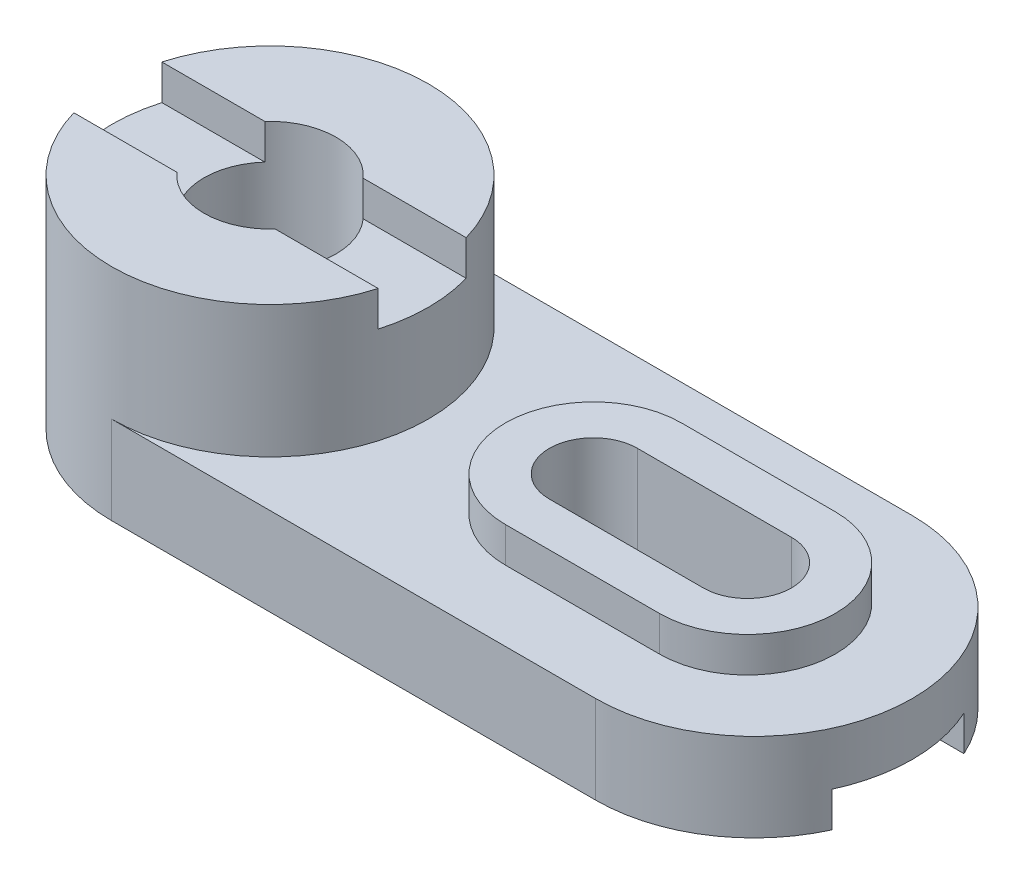
SolidWorks part; units mm, degrees
ref_plane "Front Plane" through (0, 0, 0) normal (0, 0, 1) x (1, 0, 0)
ref_plane "Top Plane" through (0, 0, 0) normal (0, 1, 0) x (1, 0, 0)
ref_plane "Right Plane" through (0, 0, 0) normal (1, 0, 0) x (0, 0, -1)
sketch "Sketch2" plane through (0, 0, 0) normal (0, 1, 0) x (1, 0, 0)
  line L0 (-55, 0) -> (55, 0) construction
  line L1 (-55, 36) -> (55, 36)
  line L2 (-55, -36) -> (55, -36)
  arc A0 (-55, 36) -> (-55, -36) centre (-55, 0) ccw
  arc A1 (55, -36) -> (55, 36) centre (55, 0) ccw
  point P2 (0, 0)
  dimension "D1" = 110
  dimension "D2" = 36
extrude "Boss-Extrude1" add sketch "Sketch2" along normal blind 20
sketch "Sketch3" plane through (0, 20, 0) normal (0, 1, 0) x (1, 0, 0)
  circle A0 centre (-55, 0) radius 36
  arc A3 (55, -36) -> (55, 36) centre (55, 0) ccw construction
  point P7 (91, 0)
  point P11 (0, 0)
  point P12 (0, 0)
  dimension "D3" = 72
  dimension "D1" = 146
extrude "Boss-Extrude2" add sketch "Sketch3" along normal blind 30 contours A0
sketch "Sketch4" plane through (0, 20, 0) normal (0, 1, 0) x (1, 0, 0)
  line L0 (18.5, 0) -> (53.5, 0) construction
  line L1 (18.5, 20) -> (53.5, 20)
  line L2 (18.5, -20) -> (53.5, -20)
  arc A0 (18.5, 20) -> (18.5, -20) centre (18.5, 0) ccw
  arc A1 (53.5, -20) -> (53.5, 20) centre (53.5, 0) ccw
  arc A3 (-55, -36) -> (-55, 36) centre (-55, 0) ccw construction
  point P2 (36, 0)
  point P8 (0, 0)
  point P14 (-19, 0)
  dimension "D2" = 20
  dimension "D1" = 35
  dimension "D3" = 55
extrude "Boss-Extrude3" add sketch "Sketch4" along normal blind 8
sketch "Sketch6" plane through (0, 0, 0) normal (1, 0, 0) x (0, 0, -1)
  line L0 (-36, 0) -> (36, 0) construction
  line L1 (-15, 0) -> (15, 0)
  line L2 (-15, 0) -> (-15, 8)
  line L3 (-15, 8) -> (15, 8)
  line L4 (15, 0) -> (15, 8)
  line L5 (0, 20) -> (0, 0) construction
  line L6 (36, 50) -> (-36, 50) construction
  line L7 (-10, 50) -> (10, 50)
  line L8 (-10, 50) -> (-10, 42)
  line L9 (-10, 42) -> (10, 42)
  line L10 (10, 50) -> (10, 42)
  line L11 (36, 20) -> (36, 50) construction
  point P6 (0, 8)
  point P11 (0, 0)
  point P18 (0, 0)
  dimension "D1" = 8
  dimension "D2" = 0
  dimension "D3" = 30
  dimension "D4" = 20
  dimension "D5" = 8
  dimension "D6" = 26
extrude "Cut-Extrude1" cut sketch "Sketch6" against normal through all both and the other way through all
sketch "Sketch7" plane through (0, 0, 0) normal (0, 1, 0) x (1, 0, 0)
  line L0 (18.5, 0) -> (53.5, 0) construction
  line L1 (18.5, 10) -> (53.5, 10)
  line L2 (18.5, -10) -> (53.5, -10)
  circle A0 centre (-55, 0) radius 15
  arc A1 (18.5, 10) -> (18.5, -10) centre (18.5, 0) ccw
  arc A2 (53.5, -10) -> (53.5, 10) centre (53.5, 0) ccw
  arc A3 (-20.4168, -10) -> (-20.4168, 10) centre (-55, 0) ccw construction
  point P5 (36, 0)
  point P14 (-19, 0)
  dimension "D1" = 10
  dimension "D4" = 30
  dimension "D2" = 35
  dimension "D3" = 55
extrude "Cut-Extrude2" cut sketch "Sketch7" against normal blind 1 and the other way through all
